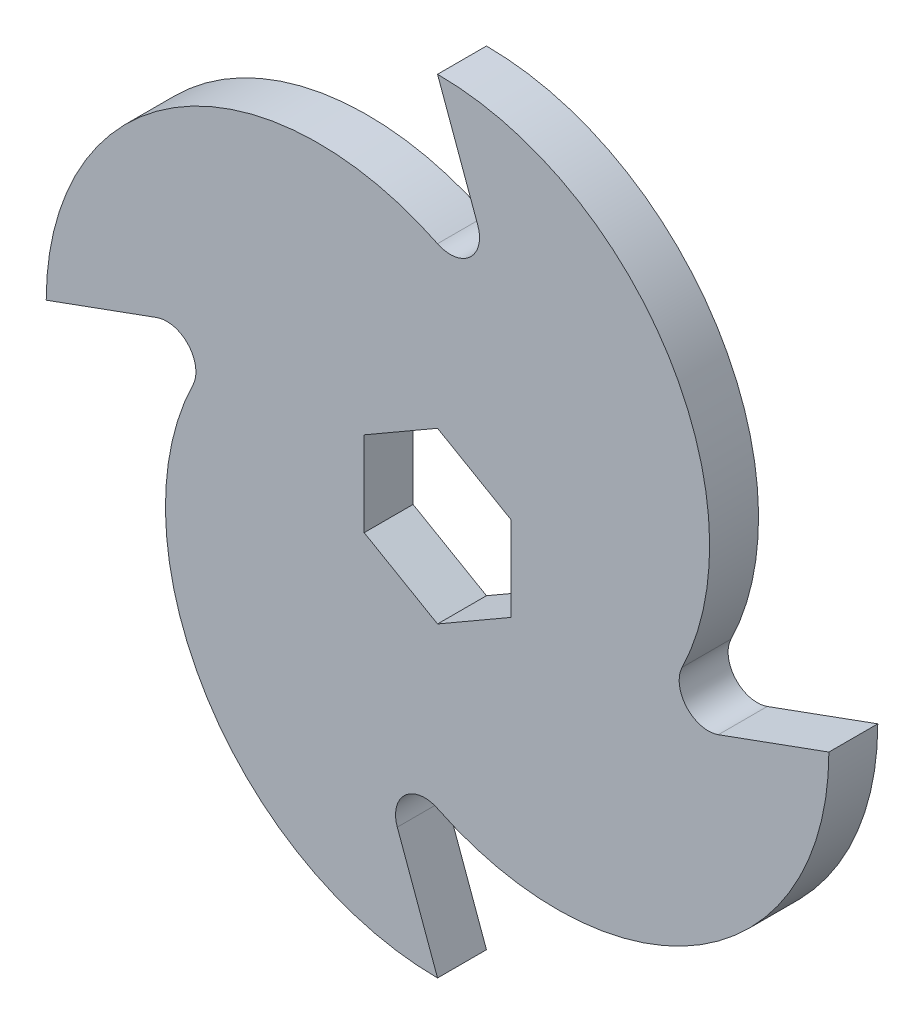
SolidWorks part; units mm, degrees
ref_plane "Front Plane" through (0, 0, 0) normal (0, 0, 1) x (1, 0, 0)
ref_plane "Top Plane" through (0, 0, 0) normal (0, 1, 0) x (1, 0, 0)
ref_plane "Right Plane" through (0, 0, 0) normal (1, 0, 0) x (0, 0, -1)
sketch "Sketch2" plane through (0, 0, 0) normal (0, 0, 1) x (1, 0, 0)
  line L0 (0, 0) -> (0, 50.8) construction
  line L1 (0, 0) -> (50.8, 0) construction
  line L2 (0, 0) -> (0, -50.8) construction
  line L3 (0, 0) -> (-50.8, 0) construction
  line L4 (0, 50.8) -> (5.222, 36.4528)
  line L5 (50.8, 0) -> (36.4528, -5.222)
  line L6 (0, -50.8) -> (-5.222, -36.4528)
  line L7 (-50.8, 0) -> (-36.4528, 5.222)
  line L9 (0, 10.9985) -> (-9.525, 5.4993)
  line L10 (-9.525, 5.4993) -> (-9.525, -5.4993)
  line L11 (-9.525, -5.4993) -> (0, -10.9985)
  line L12 (0, -10.9985) -> (9.525, -5.4993)
  line L13 (9.525, -5.4993) -> (9.525, 5.4993)
  line L14 (9.525, 5.4993) -> (0, 10.9985)
  circle A0 centre (0, 0) radius 50.8 construction
  circle A1 centre (0, 15.4781) radius 35.3219
  circle A2 centre (15.4781, 0) radius 35.3219
  circle A3 centre (0, -15.4781) radius 35.3219
  circle A4 centre (-15.4781, 0) radius 35.3219
  arc A5 (5.222, 36.4528) -> (0, 31.75) centre (1.6607, 35.1566) cw
  arc A6 (36.4528, -5.222) -> (31.75, 0) centre (35.1566, -1.6607) cw
  arc A7 (-5.222, -36.4528) -> (0, -31.75) centre (-1.6607, -35.1566) cw
  arc A8 (-36.4528, 5.222) -> (-31.75, 0) centre (-35.1566, 1.6607) cw
  circle A9 centre (0, 0) radius 9.525 construction
  point P17 (0, 0)
  point P34 (0, 0)
  dimension "D1" = 101.6
  dimension "D3" = 20
  dimension "D4" = 19.05
  dimension "D6" = 19.05
  dimension "D2" = 4
  dimension "D5" = 4
extrude "Boss-Extrude1" add sketch "Sketch2" along normal mid plane 6.35 contours A2 A5 A4 A3 A1 | L6 A7 A4 A3 | A4 A7 A2 A1 A3 | A2 A4 A1 | A3 A6 A1 A4 A2 | L5 A6 A3 A2 | A4 A1 A3 | A1 A8 A3 A2 A4 | L7 A8 A1 A4 | A2 A3 A1 | A3 A4 A2 | A1 A4 A3 A2 L14 L13 L12 L11 L10 L9 | L4 A5 A2 A1
sketch "Sketch3" plane through (0, 0, 3.175) normal (0, 0, 1) x (1, 0, 0)
  line L4 (0, -50.8) -> (-5.222, -36.4528)
  line L5 (50.8, 0) -> (36.4528, -5.222)
  line L6 (0, 50.8) -> (5.222, 36.4528)
  line L7 (-50.8, 0) -> (-36.4528, 5.222)
  line L8 (0, -50.8) -> (-5.222, -36.4528)
  line L9 (50.8, 0) -> (36.4528, -5.222)
  line L10 (0, 50.8) -> (5.222, 36.4528)
  line L11 (-50.8, 0) -> (-36.4528, 5.222)
  arc A0 (-50.8, 0) -> (-40.0197, 20.06) centre (-26.7461, 0) cw
  arc A2 (-40.0197, 20.06) -> (1.4633, 31.3719) centre (-2.1152, -37.224) cw
  arc A3 (0, 31.75) -> (5.222, 36.4528) centre (1.6607, 35.1566) ccw construction
  arc A4 (0, 31.75) -> (-50.8, 0) centre (-15.4781, 0) ccw construction
  arc A5 (20.06, 40.0197) -> (31.3719, -1.4633) centre (-37.224, 2.1152) cw
  arc A6 (0, 50.8) -> (20.06, 40.0197) centre (0, 26.7461) cw
  arc A7 (40.0197, -20.06) -> (-1.4633, -31.3719) centre (2.1152, 37.224) cw
  arc A8 (50.8, 0) -> (40.0197, -20.06) centre (26.7461, 0) cw
  arc A9 (-20.06, -40.0197) -> (-31.3719, 1.4633) centre (37.224, -2.1152) cw
  arc A10 (0, -50.8) -> (-20.06, -40.0197) centre (0, -26.7461) cw
  arc A13 (-31.75, 0) -> (-36.4528, 5.222) centre (-35.1566, 1.6607) ccw
  arc A14 (-31.75, 0) -> (0, -50.8) centre (0, -15.4781) ccw
  arc A15 (0, -31.75) -> (-5.222, -36.4528) centre (-1.6607, -35.1566) ccw
  arc A16 (0, -31.75) -> (50.8, 0) centre (15.4781, 0) ccw
  arc A17 (31.75, 0) -> (36.4528, -5.222) centre (35.1566, -1.6607) ccw
  arc A18 (31.75, 0) -> (0, 50.8) centre (0, 15.4781) ccw
  arc A19 (0, 31.75) -> (5.222, 36.4528) centre (1.6607, 35.1566) ccw
  arc A20 (0, 31.75) -> (-50.8, 0) centre (-15.4781, 0) ccw
  arc A21 (-31.75, 0) -> (-36.4528, 5.222) centre (-35.1566, 1.6607) ccw
  arc A22 (-31.75, 0) -> (0, -50.8) centre (0, -15.4781) ccw
  arc A23 (0, -31.75) -> (-5.222, -36.4528) centre (-1.6607, -35.1566) ccw
  arc A24 (0, -31.75) -> (50.8, 0) centre (15.4781, 0) ccw
  arc A25 (31.75, 0) -> (36.4528, -5.222) centre (35.1566, -1.6607) ccw
  arc A26 (31.75, 0) -> (0, 50.8) centre (0, 15.4781) ccw
  arc A27 (0, 31.75) -> (5.222, 36.4528) centre (1.6607, 35.1566) ccw
  arc A28 (0, 31.75) -> (-50.8, 0) centre (-15.4781, 0) ccw
  point P51 (0, 0)
  arc M13 (-36.4528, 5.222) -> (-31.75, 0) centre (-35.1566, 1.6607) cw
  arc M14 (-31.75, 0) -> (0, -50.8) centre (0, -15.4781) ccw
  arc M16 (-5.222, -36.4528) -> (0, -31.75) centre (-1.6607, -35.1566) cw
  arc M17 (0, -31.75) -> (50.8, 0) centre (15.4781, 0) ccw
  arc M19 (36.4528, -5.222) -> (31.75, 0) centre (35.1566, -1.6607) cw
  arc M20 (31.75, 0) -> (0, 50.8) centre (0, 15.4781) ccw
  arc M22 (5.222, 36.4528) -> (0, 31.75) centre (1.6607, 35.1566) cw
  arc M23 (0, 31.75) -> (-50.8, 0) centre (-15.4781, 0) ccw
  dimension "D1" = 0
  dimension "D2" = 4
extrude "Cut-Extrude1" [suppressed] cut sketch "Sketch3" against normal through all contours A0 A2 M22 M23 | A6 A5 M20 M19 | A8 A7 M17 M16 | A10 A9 M14 M13
